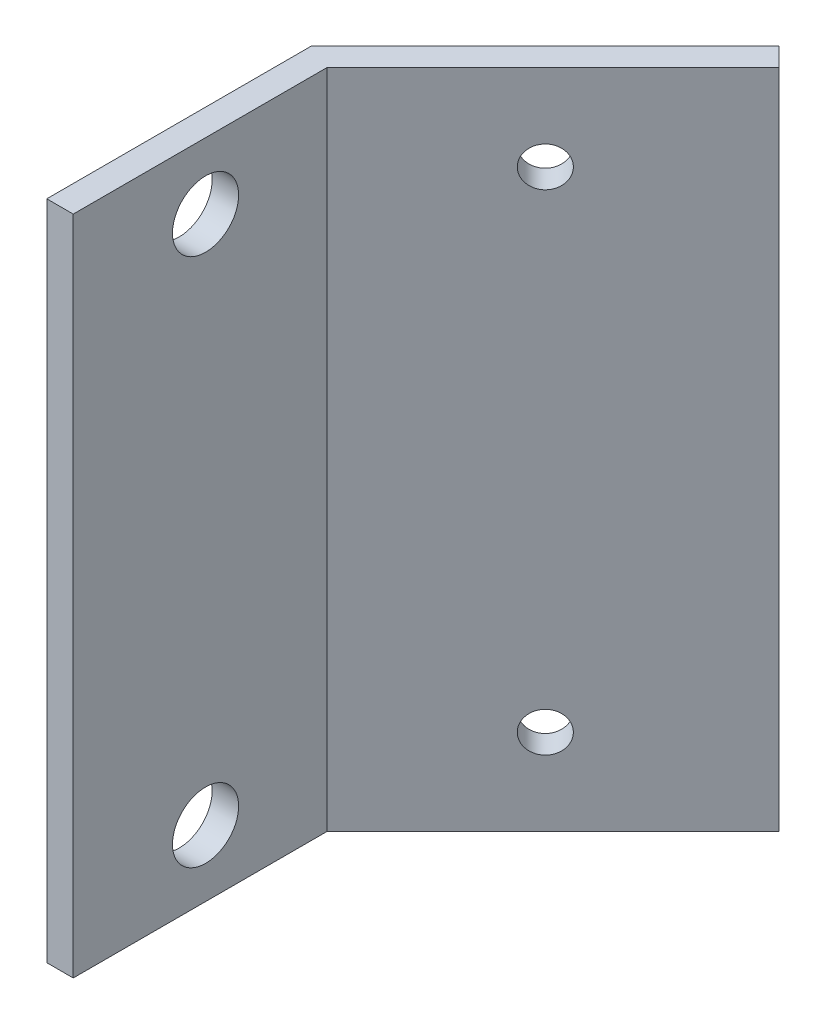
SolidWorks part; units mm, degrees
ref_plane "Plan de face" through (0, 0, 0) normal (0, 0, 1) x (1, 0, 0)
ref_plane "Plan de dessus" through (0, 0, 0) normal (0, 1, 0) x (1, 0, 0)
ref_plane "Plan de droite" through (0, 0, 0) normal (1, 0, 0) x (0, 0, -1)
sketch "Esquisse1" plane through (0, 0, 0) normal (0, 1, 0) x (1, 0, 0)
  line L0 (0, 0) -> (0, 20)
  line L1 (0, 20) -> (17.6777, 37.6777)
  line L2 (17.6777, 37.6777) -> (19.0919, 36.2635)
  line L3 (19.0919, 36.2635) -> (2, 19.1716)
  line L4 (2, 19.1716) -> (2, 0)
  line L5 (2, 0) -> (0, 0)
  dimension "D1" = 2
  dimension "D2" = 20
  dimension "D3" = 45
  dimension "D4" = 25
extrude "Extrusion1" add sketch "Esquisse1" along normal blind 50
sketch "Esquisse3" plane through (0, 0, 0) normal (-1, 0, 0) x (0, 0, 1)
  line L0 (-10, 0) -> (-10, 50) construction
  line L1 (-20, 0) -> (0, 0) construction
  line L2 (-20, 50) -> (0, 50) construction
  line L3 (0, 25) -> (-20, 25) construction
  line L4 (0, 50) -> (0, 0) construction
  line L5 (-20, 50) -> (-20, 0) construction
  line L6 (0, 5) -> (-20, 5) construction
  circle A0 centre (-10, 5) radius 2.5
  circle A1 centre (-10, 45) radius 2.5
  dimension "D1" = 5
  dimension "D2" = 5
extrude "Extrusion2" cut sketch "Esquisse3" against normal up to next
sketch "Esquisse4" plane through (-10, 0, -10) normal (-0.7071, 0, -0.7071) x (-0.7071, 0, 0.7071)
  line L0 (-26.6421, 50) -> (-26.6421, 0) construction
  line L1 (-39.1421, 50) -> (-14.1421, 50) construction
  line L2 (-39.1421, 0) -> (-14.1421, 0) construction
  line L3 (-39.1421, 25) -> (-14.1421, 25) construction
  line L4 (-39.1421, 50) -> (-39.1421, 0) construction
  line L5 (-14.1421, 50) -> (-14.1421, 0) construction
  line L6 (-39.1421, 43.5) -> (-14.1421, 43.5) construction
  circle A0 centre (-26.6421, 43.5) radius 1.5
  circle A1 centre (-26.6421, 6.5) radius 1.5
  dimension "D2" = 3
  dimension "D1" = 18.5
extrude "Extrusion3" cut sketch "Esquisse4" against normal up to next
